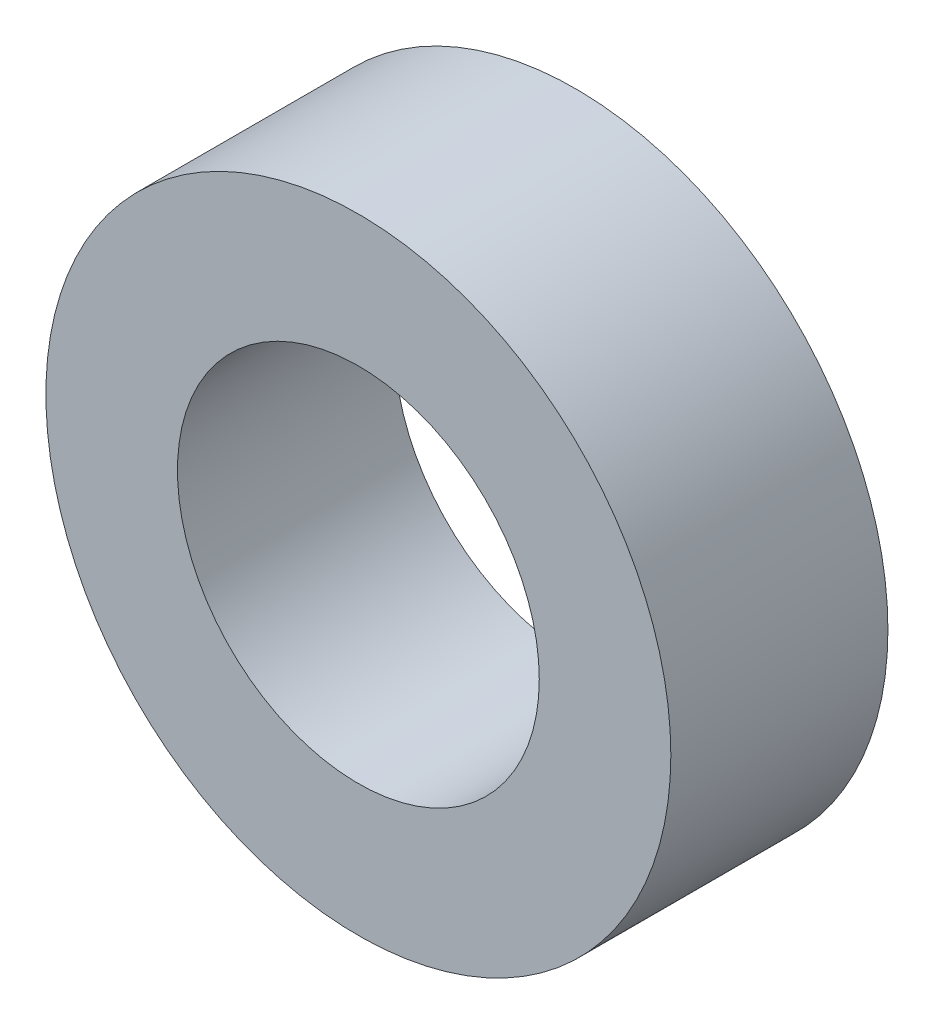
SolidWorks part; units mm, degrees
ref_plane "Front Plane" through (0, 0, 0) normal (0, 0, 1) x (1, 0, 0)
ref_plane "Top Plane" through (0, 0, 0) normal (0, 1, 0) x (1, 0, 0)
ref_plane "Right Plane" through (0, 0, 0) normal (1, 0, 0) x (0, 0, -1)
sketch "Sketch1" plane through (0, 0, 0) normal (0, 0, 1) x (1, 0, 0)
  circle A0 centre (0, 0) radius 2.75
  circle A1 centre (0, 0) radius 4.75
  dimension "D1" = 5.5
  dimension "D2" = 2
extrude "Boss-Extrude1" add sketch "Sketch1" along normal blind 3.3
